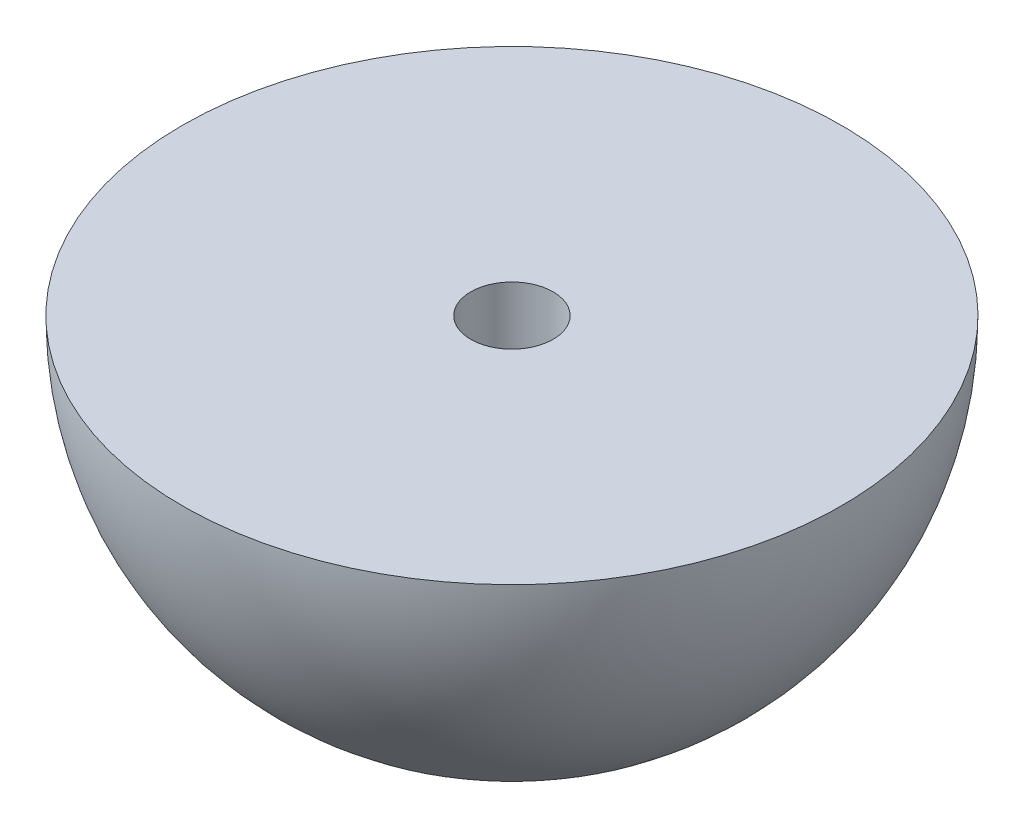
SolidWorks part; units mm, degrees
ref_plane "Plan de face" through (0, 0, 0) normal (0, 0, 1) x (1, 0, 0)
ref_plane "Plan de dessus" through (0, 0, 0) normal (0, 1, 0) x (1, 0, 0)
ref_plane "Plan de droite" through (0, 0, 0) normal (1, 0, 0) x (0, 0, -1)
sketch "Esquisse1" plane through (0, 0, 0) normal (0, 0, 1) x (1, 0, 0)
  line L0 (-8, 0) -> (0, 0)
  line L1 (0, 0) -> (0, -8)
  line L2 (0, -8) -> (-6.4726, -8) construction
  arc A1 (-8, 0) -> (0, -8) centre (0, 0) ccw
  dimension "D1" = 8
  dimension "D2" = 8
revolve "Révolution1" add sketch "Esquisse1" angle 360 about L1
sketch "Esquisse2" plane through (0, 0, 0) normal (0, 1, 0) x (1, 0, 0)
  circle A0 centre (0, 0) radius 1
  dimension "D1" = 2
extrude "Enlèv. mat.-Extru.1" cut sketch "Esquisse2" against normal through all
ref_plane "Plan1" through (0, -3, 0) normal (0, 1, 0) x (1, 0, 0)
sketch "Esquisse4" plane through (0, -3, 0) normal (0, 1, 0) x (1, 0, 0)
  line L1 (2.1673, -0.8553) -> (1.8244, 1.4493)
  line L2 (1.8244, 1.4493) -> (-0.343, 2.3046)
  line L3 (-0.343, 2.3046) -> (-2.1673, 0.8553)
  line L4 (-2.1673, 0.8553) -> (-1.8244, -1.4493)
  line L5 (-1.8244, -1.4493) -> (0.343, -2.3046)
  line L6 (0.343, -2.3046) -> (2.1673, -0.8553)
  circle A0 centre (0, 0) radius 2.0178 construction
  dimension "D1" = 2.33
extrude "Enlèv. mat.-Extru.3" cut sketch "Esquisse4" against normal through all
